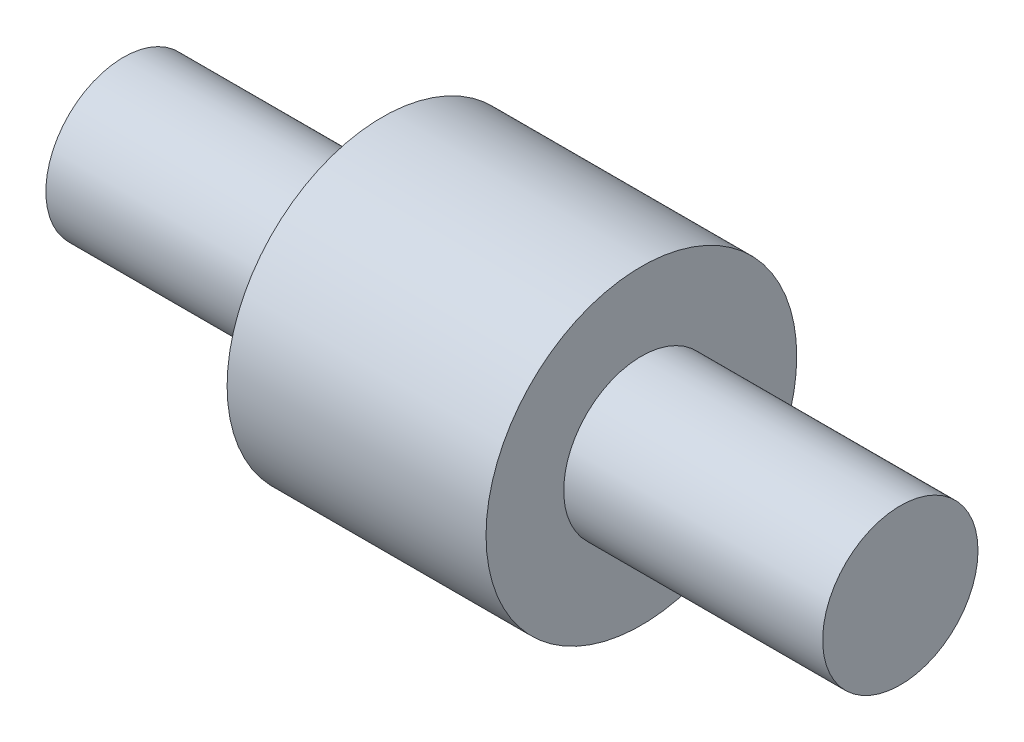
SolidWorks part; units mm, degrees
ref_plane "Plan de face" through (0, 0, 0) normal (0, 0, 1) x (1, 0, 0)
ref_plane "Plan de dessus" through (0, 0, 0) normal (0, 1, 0) x (1, 0, 0)
ref_plane "Plan de droite" through (0, 0, 0) normal (1, 0, 0) x (0, 0, -1)
sketch "Esquisse1" plane through (0, 0, 0) normal (0, 0, 1) x (1, 0, 0)
  line L0 (0, 0) -> (0, 1.5)
  line L1 (0, 1.5) -> (5, 1.5)
  line L2 (5, 1.5) -> (5, 3)
  line L3 (5, 3) -> (10, 3)
  line L4 (10, 3) -> (10, 1.5)
  line L5 (10, 1.5) -> (15, 1.5)
  line L6 (15, 1.5) -> (15, 0)
  line L7 (15, 0) -> (0, 0)
  dimension "D1" = 1.5
  dimension "D2" = 1.5
  dimension "D3" = 3
  dimension "D4" = 5
  dimension "D5" = 5
  dimension "D6" = 5
revolve "Révolution1" add sketch "Esquisse1" angle 360 about L7
